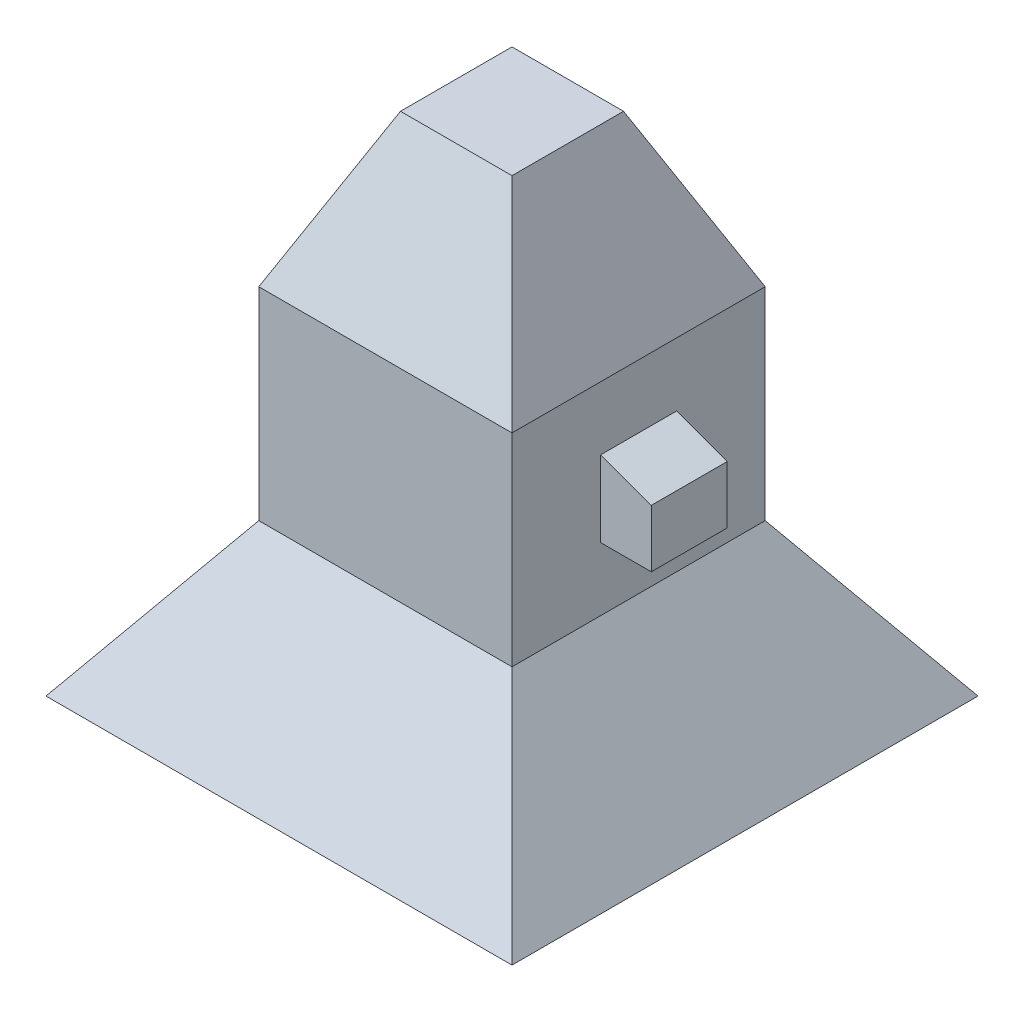
SolidWorks part; units mm, degrees
ref_plane "Front Plane" through (0, 0, 0) normal (0, 0, 1) x (1, 0, 0)
ref_plane "Top Plane" through (0, 0, 0) normal (0, 1, 0) x (1, 0, 0)
ref_plane "Right Plane" through (0, 0, 0) normal (1, 0, 0) x (0, 0, -1)
sketch "Sketch1" plane through (0, 0, 0) normal (0, 1, 0) x (1, 0, 0)
  line L1 (-50, -50) -> (50, -50)
  line L2 (-50, -50) -> (-50, 50)
  line L3 (-50, 50) -> (50, 50)
  line L4 (50, -50) -> (50, 50)
  line L5 (-50, -50) -> (50, 50) construction
  line L6 (-50, 50) -> (50, -50) construction
  point P0 (0, 0)
  dimension "D1" = 100
extrude "Boss-Extrude1" add sketch "Sketch1" along normal blind 80
sketch "Sketch2" plane through (0, 80, 0) normal (0, 1, 0) x (1, 0, 0)
  line L4 (50, -50) -> (50, 50)
  line L5 (50, 50) -> (-50, 50)
  line L6 (-50, 50) -> (-50, -50)
  line L7 (-50, -50) -> (50, -50)
  line L8 (50, -50) -> (50, 50)
  line L9 (50, 50) -> (-50, 50)
  line L10 (-50, 50) -> (-50, -50)
  line L11 (-50, -50) -> (50, -50)
  dimension "D1" = 0
extrude "Boss-Extrude2" add sketch "Sketch2" along normal blind 60 draft 25
sketch "Sketch3" plane through (0, 0, 0) normal (0, -1, 0) x (1, 0, 0)
  line L4 (50, -50) -> (50, 50)
  line L5 (50, 50) -> (-50, 50)
  line L6 (-50, 50) -> (-50, -50)
  line L7 (-50, -50) -> (50, -50)
  line L8 (50, -50) -> (50, 50)
  line L9 (50, 50) -> (-50, 50)
  line L10 (-50, 50) -> (-50, -50)
  line L11 (-50, -50) -> (50, -50)
  dimension "D1" = 0
extrude "Boss-Extrude3" add sketch "Sketch3" along normal blind 60 draft 35 draft outward yes
ref_plane "Plane1" through (0, -40, 0) normal (0, -1, 0) x (-1, 0, 0)
sketch "Sketch5" plane through (0, -40, 0) normal (0, -1, 0) x (-1, 0, 0)
  line L0 (92.0125, 92.0125) -> (-92.0125, 92.0125) construction
  line L1 (-72.0125, -72.0125) -> (72.0125, -72.0125)
  line L2 (-72.0125, -72.0125) -> (-72.0125, 72.0125)
  line L3 (-72.0125, 72.0125) -> (72.0125, 72.0125)
  line L4 (72.0125, -72.0125) -> (72.0125, 72.0125)
  line L5 (-72.0125, -72.0125) -> (72.0125, 72.0125) construction
  line L6 (-72.0125, 72.0125) -> (72.0125, -72.0125) construction
  point P0 (0, 0)
  dimension "D1" = 20
extrude "Cut-Extrude2" cut sketch "Sketch5" along normal blind 20 draft 35 draft outward yes
sketch "Sketch6" plane through (50, 0, 0) normal (1, 0, 0) x (0, 0, -1)
  line L0 (0, 80) -> (0, 0) construction
  line L1 (-15, 25) -> (15, 25)
  line L2 (-15, 25) -> (-15, 55)
  line L3 (-15, 55) -> (15, 55)
  line L4 (15, 25) -> (15, 55)
  line L5 (-15, 25) -> (15, 55) construction
  line L6 (-15, 55) -> (15, 25) construction
  line L7 (-50, 80) -> (50, 80) construction
  line L8 (-50, 80) -> (-50, 0) construction
  line L9 (-50, 40) -> (50, 40) construction
  line L10 (50, 80) -> (50, 0) construction
  point P0 (0, 40)
  point P16 (0, 40)
  dimension "D1" = 30
extrude "Boss-Extrude4" add sketch "Sketch6" along normal blind 20
draft "Draft5" type of draft neutral plane draft angle 20 faces to draft 1 face at (60, 55, 0) neutral plane through (50, 80, 50) neutral plane normal (1, 0, 0) parameters "D1"=20
